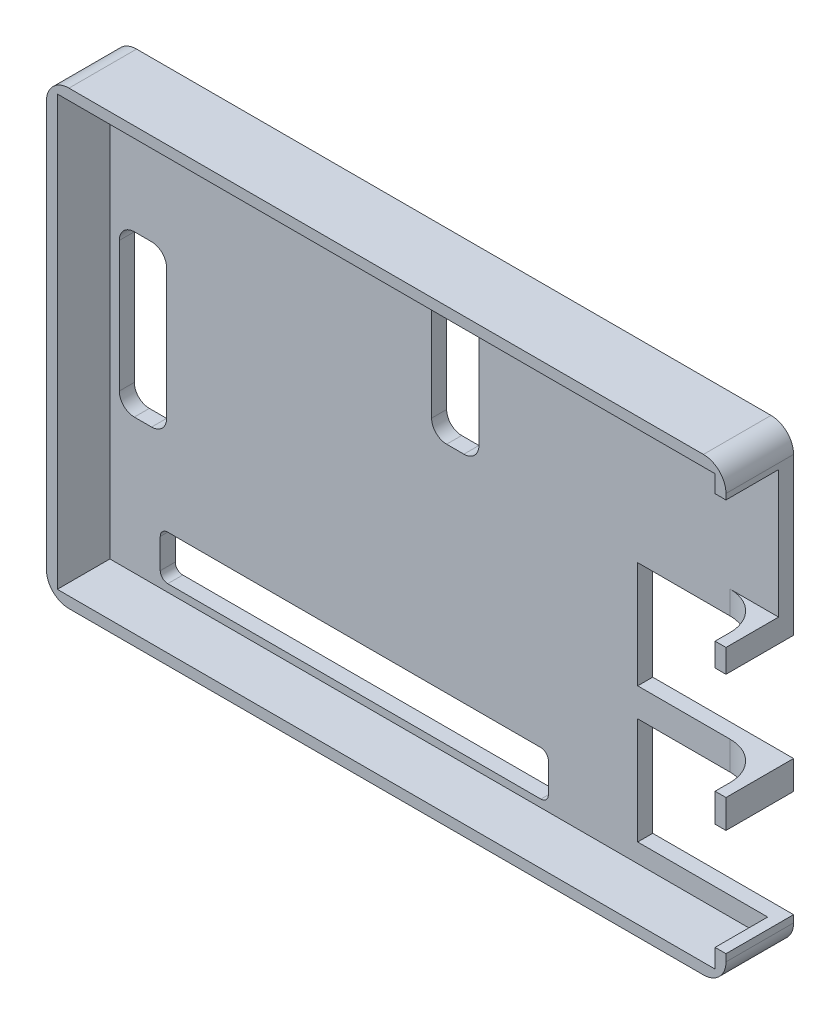
SolidWorks part; units mm, degrees
ref_plane "Alzado" through (0, 0, 0) normal (0, 0, 1) x (1, 0, 0)
ref_plane "Planta" through (0, 0, 0) normal (0, 1, 0) x (1, 0, 0)
ref_plane "Vista lateral" through (0, 0, 0) normal (1, 0, 0) x (0, 0, -1)
sketch "Croquis1" plane through (0, 0, 0) normal (0, 0, 1) x (1, 0, 0)
  line L1 (-45.225, -30) -> (45.225, -30)
  line L2 (-45.225, -30) -> (-45.225, 30)
  line L3 (-45.225, 30) -> (45.225, 30)
  line L4 (45.225, -30) -> (45.225, 30)
  line L5 (-45.225, -30) -> (45.225, 30) construction
  line L6 (-45.225, 30) -> (45.225, -30) construction
  point P0 (0, 0)
  dimension "D1" = 60
  dimension "D2" = 90.45
extrude "Saliente-Extruir1" add sketch "Croquis1" against normal blind 2
sketch "Croquis2" plane through (0, 0, 0) normal (0, 0, 1) x (1, 0, 0)
  line L0 (45.225, 30) -> (-45.225, 30) construction
  line L1 (-43.775, -28.55) -> (43.775, -28.55)
  line L2 (-43.775, -28.55) -> (-43.775, 28.55)
  line L3 (-43.775, 28.55) -> (43.775, 28.55)
  line L4 (43.775, -28.55) -> (43.775, 28.55)
  line L5 (-43.775, -28.55) -> (43.775, 28.55) construction
  line L6 (-43.775, 28.55) -> (43.775, -28.55) construction
  line L7 (45.225, -30) -> (45.225, 30) construction
  line L9 (45.225, -30) -> (-45.225, -30)
  line L10 (45.225, -30) -> (45.225, 30)
  line L11 (45.225, 30) -> (-45.225, 30)
  line L12 (-45.225, -30) -> (-45.225, 30)
  line L13 (45.225, -30) -> (-45.225, 30) construction
  line L14 (45.225, 30) -> (-45.225, -30) construction
  point P0 (0, 0)
  point P10 (0, 0)
  dimension "D1" = 1.45
  dimension "D2" = 1.45
extrude "Saliente-Extruir2" add sketch "Croquis2" along normal blind 7
sketch "Croquis3" plane through (0, 0, -2) normal (0, 0, -1) x (-1, 0, 0)
  line L0 (-45.225, -30) -> (-45.225, 30) construction
  line L1 (-45.225, -26.05) -> (-26.475, -26.05)
  line L2 (-45.225, -26.05) -> (-45.225, -11.85)
  line L3 (-45.225, -11.85) -> (-26.475, -11.85)
  line L4 (-26.475, -26.05) -> (-26.475, -11.85)
  line L5 (45.225, -30) -> (-45.225, -30) construction
  line L6 (-45.225, -8.05) -> (-26.475, -8.05)
  line L7 (-45.225, -8.05) -> (-45.225, 6.15)
  line L8 (-45.225, 6.15) -> (-26.475, 6.15)
  line L9 (-26.475, -8.05) -> (-26.475, 6.15)
  dimension "D1" = 14.2
  dimension "D2" = 18.75
  dimension "D3" = 3.95
  dimension "D4" = 21.95
extrude "Cortar-Extruir1" cut sketch "Croquis3" against normal up to surface (9 mm away) up to face at (0, 0, 7)
sketch "Croquis4" plane through (45.225, 0, 0) normal (1, 0, 0) x (0, 0, -1)
  line L0 (-7, 6.15) -> (-7, 30) construction
  line L1 (-7, 9.25) -> (0, 9.25)
  line L2 (-7, 9.25) -> (-7, 26.25)
  line L3 (-7, 26.25) -> (0, 26.25)
  line L4 (0, 9.25) -> (0, 26.25)
  line L5 (0, 28.55) -> (0, -28.55) construction
  line L6 (2, 30) -> (-7, 30) construction
  dimension "D1" = 17
  dimension "D2" = 3.75
extrude "Cortar-Extruir2" cut sketch "Croquis4" against normal up to next
fillet "Redondeo2" radius 3 4 edges at (45.225, -30, 2.5) (45.225, 30, 2.5) (-45.225, 30, 2.5) (-45.225, -30, 2.5)
sketch "Croquis5" plane through (0, 0, -2) normal (0, 0, -1) x (-1, 0, 0)
  line L0 (11.245, -21.61) -> (11.245, -27.55) construction
  line L1 (-14.585, -27.55) -> (37.075, -27.55)
  line L2 (-14.585, -27.55) -> (-14.585, -21.61)
  line L3 (-14.585, -21.61) -> (37.075, -21.61)
  line L4 (37.075, -27.55) -> (37.075, -21.61)
  line L5 (-14.585, -24.58) -> (37.075, -24.58) construction
  line L7 (42.225, -30) -> (-42.225, -30) construction
  line L9 (45.225, 27) -> (45.225, -27) construction
  dimension "D1" = 5.94
  dimension "D2" = 51.66
  dimension "D3" = 5.42
  dimension "D4" = 33.98
extrude "Cortar-Extruir3" cut sketch "Croquis5" against normal up to surface (2 mm away) up to face at (28.6875, -0.5375, 0)
sketch "Croquis6" plane through (0, 0, -2) normal (0, 0, -1) x (-1, 0, 0)
  line L0 (39.375, 10.79) -> (39.375, -10.57) construction
  line L1 (36.225, 10.79) -> (42.525, 10.79)
  line L2 (36.225, 10.79) -> (36.225, -10.57)
  line L3 (36.225, -10.57) -> (42.525, -10.57)
  line L4 (42.525, 10.79) -> (42.525, -10.57)
  line L5 (-5.345, 28.45) -> (0.955, 28.45)
  line L6 (-5.345, 28.45) -> (-5.345, 7.09)
  line L7 (-5.345, 7.09) -> (0.955, 7.09)
  line L8 (0.955, 28.45) -> (0.955, 7.09)
  line L9 (36.225, 0.11) -> (42.525, 0.11) construction
  line L10 (-42.225, 30) -> (42.225, 30) construction
  line L11 (45.225, 27) -> (45.225, -27) construction
  line L13 (-2.195, 28.45) -> (-2.195, 7.09) construction
  line L14 (-5.345, 17.77) -> (0.955, 17.77) construction
  line L15 (42.225, -30) -> (-42.225, -30) construction
  dimension "D1" = 21.36
  dimension "D2" = 6.3
  dimension "D3" = 5.85
  dimension "D4" = 19.21
  dimension "D6" = 47.42
  dimension "D7" = 47.77
extrude "Cortar-Extruir4" cut sketch "Croquis6" against normal up to surface (2 mm away) up to face at (-11.245, -24.58, 0)
fillet "Redondeo3" radius 2 8 edges at (5.345, 28.45, -1) (-0.955, 28.45, -1) (-0.955, 7.09, -1) (5.345, 7.09, -1) (-36.225, -10.57, -1) (-36.225, 10.79, -1) (-42.525, 10.79, -1) (-42.525, -10.57, -1)
fillet "Redondeo4" radius 1 4 edges at (-37.075, -21.61, -1) (-37.075, -27.55, -1) (14.585, -27.55, -1) (14.585, -21.61, -1)
fillet "Redondeo5" radius 5 2 edges at (43.775, 7.7, 0) (43.775, -9.95, 0)
